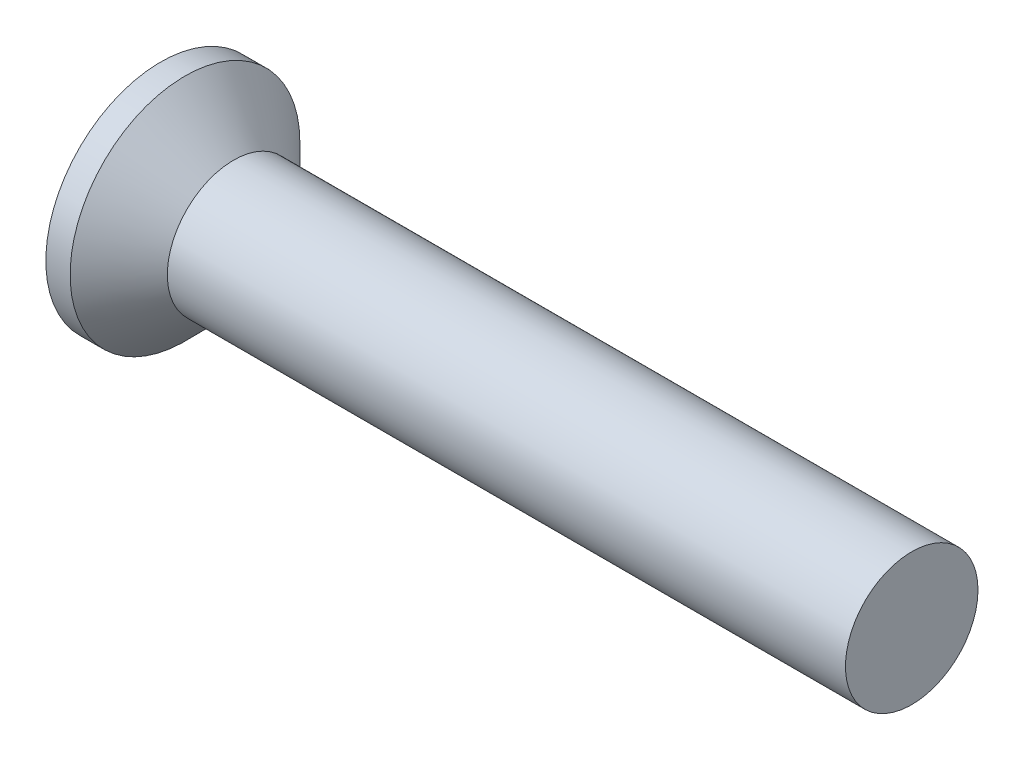
SolidWorks part; units mm, degrees
ref_plane "Front" through (0, 0, 0) normal (0, 0, 1) x (1, 0, 0)
ref_plane "Top" through (0, 0, 0) normal (0, 1, 0) x (1, 0, 0)
ref_plane "Right" through (0, 0, 0) normal (1, 0, 0) x (0, 0, -1)
sketch "Sketch1" plane through (0, 0, 0) normal (0, 0, 1) x (1, 0, 0)
  line L0 (17, 1.5) -> (2.65, 1.5)
  line L1 (2.65, 1.5) -> (1.65, 1.5)
  line L2 (1.65, 1.5) -> (0.55, 2.6)
  line L3 (0.55, 2.6) -> (0, 2.6)
  line L4 (17, 1.5) -> (17, 0)
  line L5 (4.5158, 0) -> (-89.8219, 0) construction
  line L6 (17, 0) -> (0, 0)
  line L7 (0, 2.6) -> (0, 0)
  dimension "d" = 3
  dimension "D1" = 45
  dimension "dk" = 5.2
  dimension "k" = 1.65
  dimension "l" = 17
  dimension "a" = 1
revolve "Base" add sketch "Sketch1" angle 360 about L5
cosmetic thread "ThreadCosmetic1" parameters "bb"=14.35, "THD_MINOR"=2.459
sketch "Sketch6" plane through (0, 0, 0) normal (1, 0, 0) x (0, 0, -1)
  line L0 (-1.9271, 0) -> (2.0512, 0) construction
  line L1 (0, 1.8651) -> (0, -2.0207) construction
  line L2 (0.32, 0.32) -> (0.32, 1.6)
  line L3 (0.32, 1.6) -> (-0.32, 1.6)
  line L4 (-0.32, 0.32) -> (-0.32, 1.6)
  line L5 (0.32, 0.32) -> (1.6, 0.32)
  line L6 (1.6, 0.32) -> (1.6, -0.32)
  line L7 (-1.6, 0.32) -> (-1.6, -0.32)
  line L8 (-0.32, 0.32) -> (-1.6, 0.32)
  line L9 (-0.32, -0.32) -> (-1.6, -0.32)
  line L10 (0.32, -0.32) -> (1.6, -0.32)
  line L11 (-0.32, -0.32) -> (-0.32, -1.6)
  line L12 (0.32, -1.6) -> (-0.32, -1.6)
  line L13 (0.32, -0.32) -> (0.32, -1.6)
  point P16 (-1.6, 0)
  point P17 (1.6, 0)
extrude "CrossRecess" cut sketch "Sketch6" along normal blind 0.825
draft "Draft9" type of draft neutral plane draft angle 30 faces to draft 4 face at (0.4125, 1.6, 0) face at (0.4125, 0, 1.6) face at (0.4125, -1.6, 0) face at (0.4125, 0, -1.6) neutral plane through (0, 2.6, 0) neutral plane normal (-1, 0, 0) parameters "D1"=30
fillet "Fillet5" radius 0.3 4 edges at (0.4125, -0.32, -0.32) (0.4125, 0.32, -0.32) (0.4125, 0.32, 0.32) (0.4125, -0.32, 0.32)
sketch "Sketch7" plane through (0, 0, 0) normal (1, 0, 0) x (0, 0, -1)
  line L0 (-2.0126, 0) -> (1.9757, 0) construction
  line L1 (0, 1.9314) -> (0, -2.0126) construction
  line L2 (0, 0) -> (1.5555, 1.5555) construction
  line L3 (0, 0.4782) -> (1.1314, 1.1314)
  line L4 (-1.5402, 1.5402) -> (0, 0) construction
  line L5 (0.4782, 0) -> (1.1314, 1.1314)
  line L6 (0, -0.4782) -> (1.1314, -1.1314)
  line L7 (0.4782, 0) -> (1.1314, -1.1314)
  line L8 (-0.4782, 0) -> (-1.1314, -1.1314)
  line L9 (0, -0.4782) -> (-1.1314, -1.1314)
  line L10 (-0.4782, 0) -> (-1.1314, 1.1314)
  line L11 (0, 0.4782) -> (-1.1314, 1.1314)
  dimension "D3" = 15
  dimension "m" = 3.2
extrude "Cut-Extrude3" [suppressed] cut sketch "Sketch7" along normal blind 10 draft 20
sketch "Sketch8" plane through (0, 0, 0) normal (0, 0, 1) x (1, 0, 0)
  line L0 (-8, 1.7705) -> (-9.25, 1.5)
  line L1 (-9.25, 1.5) -> (1.65, 1.5)
  line L3 (17, -1.5) -> (17, 1.5) construction
  line L6 (1.65, 1.5) -> (1.65, 6.5)
  line L7 (1.65, 6.5) -> (-8, 6.5)
  line L8 (-8, 6.5) -> (-8, 1.7705)
  line L9 (62.4753, 0.2705) -> (52.9594, 0.2705) construction
  dimension "D1" = 5
  dimension "x" = 1.25
  dimension "d" = 3
  dimension "THD_MINOR" = 2.459
  dimension "b" = 25
sketch "Sketch9" plane through (0, 0, 0) normal (0, 0, 1) x (1, 0, 0)
  line L0 (17, 1.2657) -> (17.1353, 1.5)
  line L1 (17.1353, 1.5) -> (17.1353, 1.7705)
  line L2 (17.1353, 1.7705) -> (16.8648, 1.7705)
  line L3 (16.8648, 1.7705) -> (16.8648, 1.5)
  line L4 (16.8648, 1.5) -> (17, 1.2657)
  line L5 (0, 0) -> (73.843, 0) construction
  line L6 (17, -1.5) -> (17, 1.5) construction
  dimension "D1" = 3
  dimension "D2" = 0.2705
revolve "Cut-Revolve10" [suppressed] cut sketch "Sketch9" angle 360 about L5
pattern_linear "LPattern10" [suppressed] count 44 spacing 0.3246 along (1, 0, 0)
equation "\"D1@Sketch6\" = \"m@Sketch6\" / 5"
equation "\"D1@CrossRecess\" = \"k@Sketch1\" / 2"
equation "\"D1@Sketch9\" = \"d@Sketch1\""
equation "\"D2@Sketch9\" =  ( \"d@Sketch1\" - \"THD_MINOR@ThreadCosmetic1\" )  / 2"
equation "\"D3@LPattern10\" = \"D2@Sketch9\" * 1.2"
equation "\"D1@LPattern10\" = \"bb@ThreadCosmetic1\" / \"D3@LPattern10\" "
